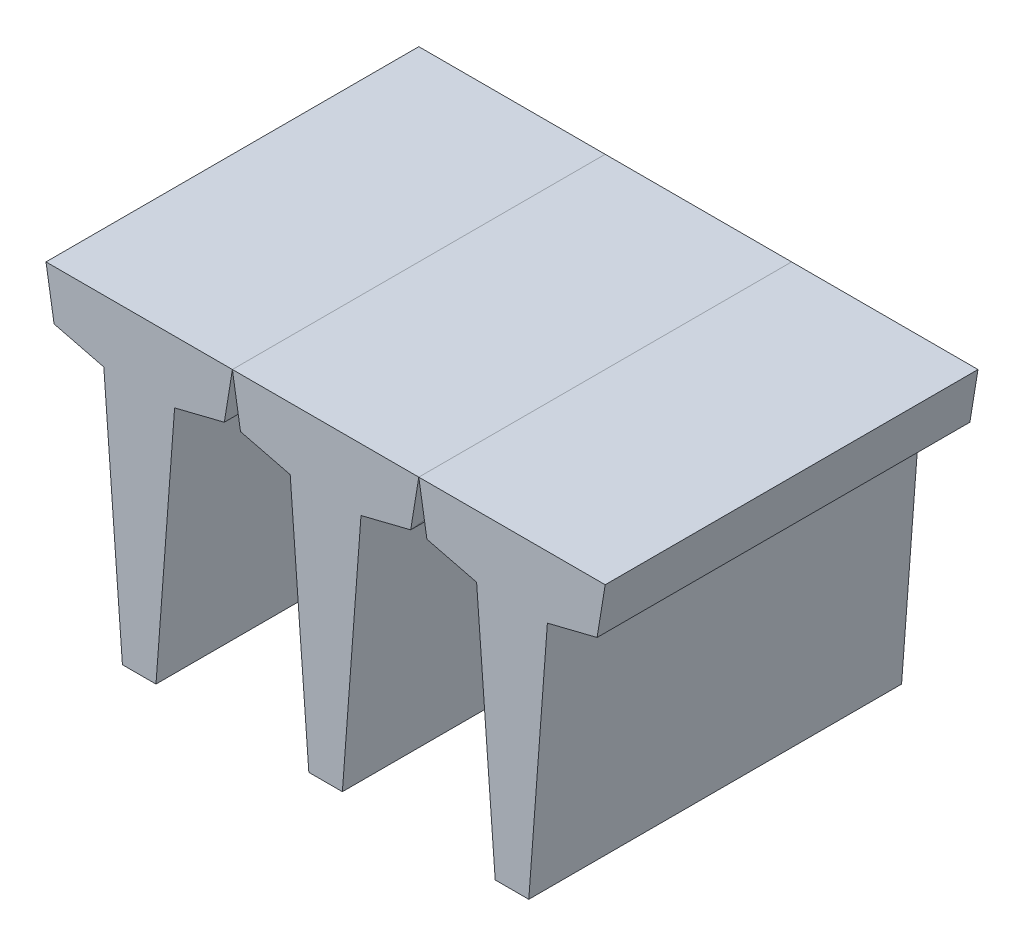
SolidWorks part; units mm, degrees
ref_plane "Front Plane" through (0, 0, 0) normal (0, 0, 1) x (1, 0, 0)
ref_plane "Top Plane" through (0, 0, 0) normal (0, 1, 0) x (1, 0, 0)
ref_plane "Right Plane" through (0, 0, 0) normal (1, 0, 0) x (0, 0, -1)
sketch "Sketch1" plane through (0, 0, 0) normal (0, 0, 1) x (1, 0, 0)
  line L0 (-135.0243, -1848.6278) -> (135.0243, -1848.6278)
  line L1 (135.0243, -1848.6278) -> (284.8088, 151.3722)
  line L2 (284.8088, 151.3722) -> (684.8088, 251.3722)
  line L3 (684.8088, 251.3722) -> (750, 651.3722)
  line L4 (750, 651.3722) -> (-750, 651.3722)
  line L5 (0, 651.3722) -> (0, -1848.6278)
  line L6 (-684.8088, 251.3722) -> (-750, 651.3722)
  line L7 (-284.8088, 151.3722) -> (-684.8088, 251.3722)
  line L8 (-135.0243, -1848.6278) -> (-284.8088, 151.3722)
  dimension "D1" = 1500
  dimension "D2" = 2500
  dimension "D3" = 500
  dimension "D4" = 400
  dimension "D5" = 400
extrude "Boss-Extrude1" add sketch "Sketch1" along normal blind 3000 contours L8 L0 L5 L4 L6 L7 | L4 L5 L0 L1 L2 L3
pattern_linear "LPattern1" count 2 spacing 1500 along (1, 0, 0) count 2 spacing 1500 along (-1, 0, 0) of bodies 101
